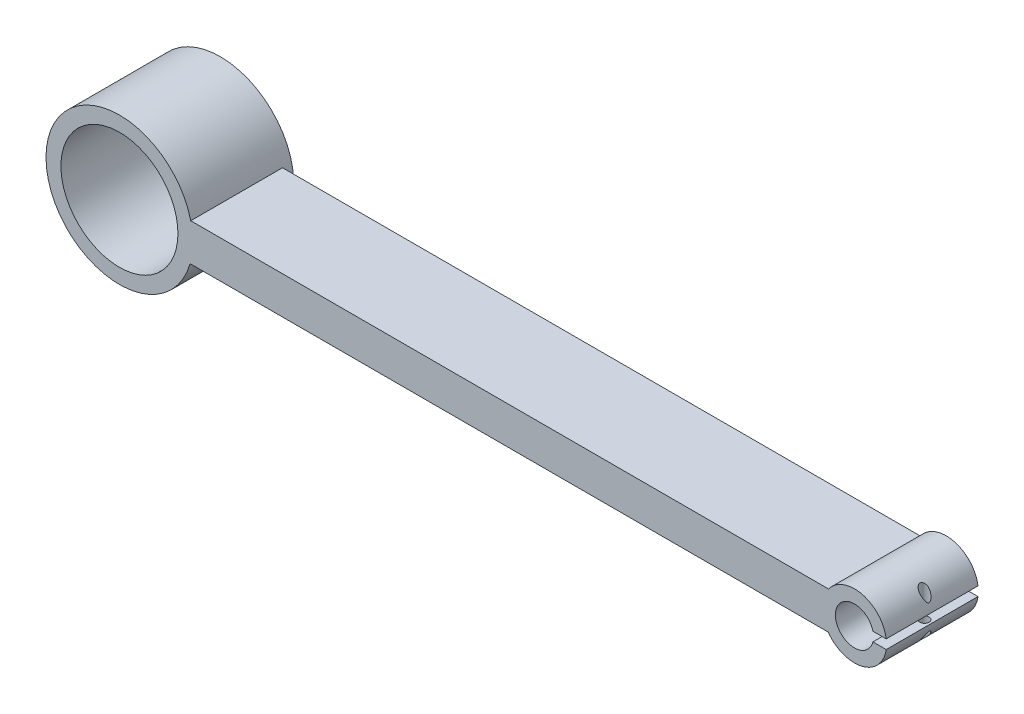
SolidWorks part; units mm, degrees
ref_plane "Plan de face" through (0, 0, 0) normal (0, 0, 1) x (1, 0, 0)
ref_plane "Plan de dessus" through (0, 0, 0) normal (0, 1, 0) x (1, 0, 0)
ref_plane "Plan de droite" through (0, 0, 0) normal (1, 0, 0) x (0, 0, -1)
sketch "Sketch1" plane through (0, 0, 0) normal (0, 0, 1) x (1, 0, 0)
  line L0 (-160.1908, 7.0254) -> (-21.1387, 7.0254)
  line L2 (-160.0431, 15.196) -> (-21.0638, 15.196)
  arc A0 (-160.0431, 15.196) -> (-160.1908, 7.0254) centre (-175.5839, 11.3903) ccw
  arc A1 (-21.0638, 15.196) -> (-21.1387, 7.0254) centre (-15.4174, 11.0586) cw
  circle A2 centre (-15.4174, 11.0586) radius 4.15
  circle A3 centre (-175.5839, 11.3903) radius 12.75
  point P8 (-95.5839, 11.3903)
  dimension "D1" = 25.5
  dimension "D2" = 8.1719
  dimension "D3" = 7
  dimension "D4" = 8.3
  dimension "D5" = 16
  dimension "D6" = 80
extrude "Boss-Extrude1" add sketch "Sketch1" along normal blind 20
sketch "Sketch2" plane through (0, 0, 0) normal (0, 0, -1) x (-1, 0, 0)
  line L0 (175.5839, 11.3903) -> (159.5839, 11.3903) construction
  line L1 (159.5839, 11.3903) -> (191.5839, 11.3903) construction
  circle A0 centre (175.5839, 11.3903) radius 16
  circle A2 centre (175.5839, 11.3903) radius 3.75
  circle A7 centre (184.0839, 11.3903) radius 1.5
  circle A9 centre (167.0839, 11.3903) radius 1.5
  dimension "D1" = 32
  dimension "D3" = 8.5
  dimension "D4" = 3
  dimension "D5" = 8.5
  dimension "D9" = 7.5
  dimension "D2" = 3
extrude "Boss-Extrude2" add sketch "Sketch2" along normal blind 2
sketch "Sketch3" plane through (0, 0, 20) normal (0, 0, 1) x (1, 0, 0)
  line L10 (-15.4174, 11.0586) -> (-7.7453, 11.0586) construction
  line L16 (-12.5236, 10.0557) -> (-7.4304, 10.0557)
  line L17 (-12.5236, 10.0557) -> (-12.5236, 12.0616)
  line L18 (-12.5236, 12.0616) -> (-7.4304, 12.0616)
  line L19 (-7.4304, 10.0557) -> (-7.4304, 12.0616)
  line L20 (-12.5236, 10.0557) -> (-7.4304, 12.0616) construction
  line L21 (-12.5236, 12.0616) -> (-7.4304, 10.0557) construction
  point P2 (-9.977, 11.0586)
  dimension "D1" = 2.0059
  dimension "D2" = 5.0932
extrude "Cut-Extrude1" cut sketch "Sketch3" against normal through all
sketch "Sketch5" plane through (0, 10.0557, 0) normal (0, 1, 0) x (1, 0, 0)
  circle A0 centre (-9.9623, -10.1864) radius 1
  dimension "D1" = 2
extrude "Cut-Extrude2" cut sketch "Sketch5" against normal through all both and the other way through all
